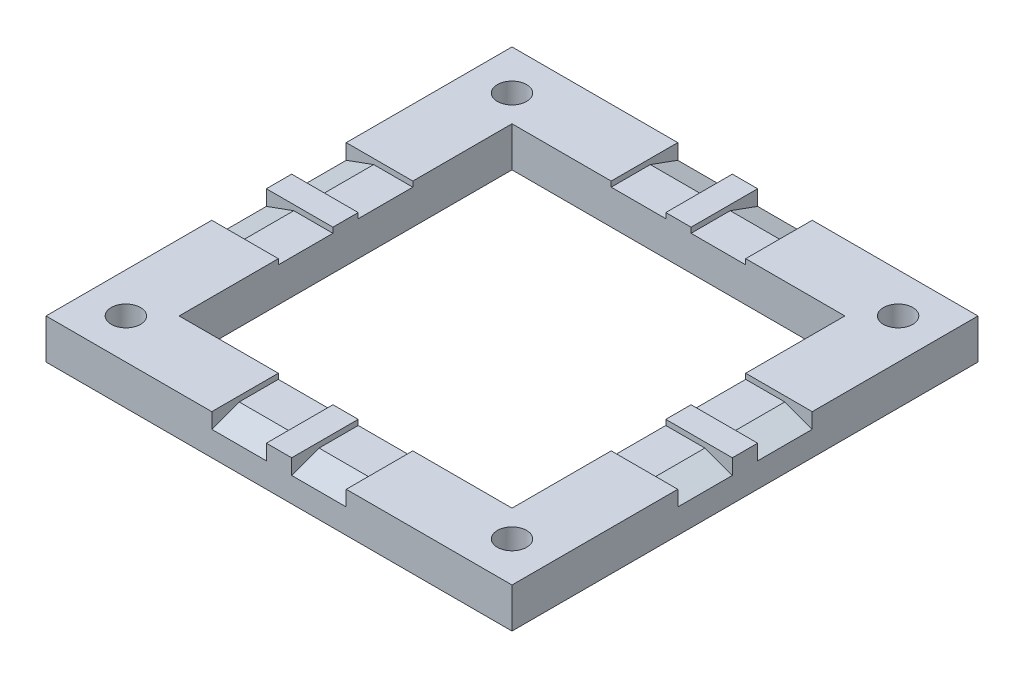
SolidWorks part; units mm, degrees
ref_plane "Front Plane" through (0, 0, 0) normal (0, 0, 1) x (1, 0, 0)
ref_plane "Top Plane" through (0, 0, 0) normal (0, 1, 0) x (1, 0, 0)
ref_plane "Right Plane" through (0, 0, 0) normal (1, 0, 0) x (0, 0, -1)
sketch "Sketch1" plane through (0, 0, 0) normal (0, 1, 0) x (1, 0, 0)
  line L1 (-17.5, -17.5) -> (17.5, -17.5)
  line L2 (-17.5, -17.5) -> (-17.5, 17.5)
  line L3 (-17.5, 17.5) -> (17.5, 17.5)
  line L4 (17.5, -17.5) -> (17.5, 17.5)
  line L5 (-17.5, -17.5) -> (17.5, 17.5) construction
  line L6 (-17.5, 17.5) -> (17.5, -17.5) construction
  point P0 (0, 0)
  dimension "D1" = 35
extrude "Boss-Extrude1" add sketch "Sketch1" along normal blind 3
sketch "Sketch3" plane through (0, 3, 0) normal (0, 1, 0) x (1, 0, 0)
  line L1 (-12.5, -12.5) -> (12.5, -12.5)
  line L2 (-12.5, -12.5) -> (-12.5, 12.5)
  line L3 (-12.5, 12.5) -> (12.5, 12.5)
  line L4 (12.5, -12.5) -> (12.5, 12.5)
  line L5 (-12.5, -12.5) -> (12.5, 12.5) construction
  line L6 (-12.5, 12.5) -> (12.5, -12.5) construction
  point P0 (0, 0)
  dimension "D1" = 25
extrude "Cut-Extrude1" cut sketch "Sketch3" against normal through all
sketch "Sketch4" plane through (0, 3, 0) normal (0, 1, 0) x (1, 0, 0)
  line L0 (-17.5, 17.5) -> (-17.5, -17.5) construction
  line L1 (-17.5, 5.05) -> (-12.5, 5.05)
  line L2 (-17.5, 5.05) -> (-17.5, 0.95)
  line L3 (-17.5, 0.95) -> (-12.5, 0.95)
  line L4 (-12.5, 5.05) -> (-12.5, 0.95)
  line L5 (-12.5, 12.5) -> (-12.5, -12.5) construction
  line L6 (17.5, 17.5) -> (-17.5, 17.5) construction
  line L7 (-5.05, 17.5) -> (-0.95, 17.5)
  line L8 (-5.05, 17.5) -> (-5.05, 12.5)
  line L9 (-5.05, 12.5) -> (-0.95, 12.5)
  line L10 (-0.95, 17.5) -> (-0.95, 12.5)
  line L11 (12.5, 12.5) -> (-12.5, 12.5) construction
  line L12 (0, 0) -> (0, 27.0615) construction
  line L13 (-23.33, 0) -> (0, 0) construction
  line L14 (0.95, 17.5) -> (0.95, 12.5)
  line L15 (5.05, 12.5) -> (0.95, 12.5)
  line L16 (5.05, 17.5) -> (5.05, 12.5)
  line L17 (5.05, 17.5) -> (0.95, 17.5)
  line L18 (12.5, 5.05) -> (12.5, 0.95)
  line L19 (17.5, 0.95) -> (12.5, 0.95)
  line L20 (17.5, 5.05) -> (17.5, 0.95)
  line L21 (17.5, 5.05) -> (12.5, 5.05)
  line L22 (17.5, -5.05) -> (12.5, -5.05)
  line L23 (17.5, -5.05) -> (17.5, -0.95)
  line L24 (17.5, -0.95) -> (12.5, -0.95)
  line L25 (12.5, -5.05) -> (12.5, -0.95)
  line L26 (5.05, -17.5) -> (0.95, -17.5)
  line L27 (5.05, -17.5) -> (5.05, -12.5)
  line L28 (5.05, -12.5) -> (0.95, -12.5)
  line L29 (0.95, -17.5) -> (0.95, -12.5)
  line L30 (-0.95, -17.5) -> (-0.95, -12.5)
  line L31 (-5.05, -12.5) -> (-0.95, -12.5)
  line L32 (-5.05, -17.5) -> (-5.05, -12.5)
  line L33 (-5.05, -17.5) -> (-0.95, -17.5)
  line L34 (-12.5, -5.05) -> (-12.5, -0.95)
  line L35 (-17.5, -0.95) -> (-12.5, -0.95)
  line L36 (-17.5, -5.05) -> (-17.5, -0.95)
  line L37 (-17.5, -5.05) -> (-12.5, -5.05)
  dimension "D1" = 1.9
  dimension "D2" = 1.9
  dimension "D3" = 4.1
extrude "Cut-Extrude2" cut sketch "Sketch4" against normal blind 0.4
chamfer "Chamfer1" distance 0.75 angle 70 8 edges at (-17.5, 2.6, -3) (-17.5, 2.6, 3) (-3, 2.6, 17.5) (3, 2.6, 17.5) (17.5, 2.6, 3) (17.5, 2.6, -3) (3, 2.6, -17.5) (-3, 2.6, -17.5)
sketch "Sketch6" plane through (0, 3, 0) normal (0, 1, 0) x (1, 0, 0)
  line L1 (-14.5, -14.5) -> (14.5, -14.5) construction
  line L2 (-14.5, -14.5) -> (-14.5, 14.5) construction
  line L3 (-14.5, 14.5) -> (14.5, 14.5) construction
  line L4 (14.5, -14.5) -> (14.5, 14.5) construction
  line L5 (-14.5, -14.5) -> (14.5, 14.5) construction
  line L6 (-14.5, 14.5) -> (14.5, -14.5) construction
  circle A0 centre (14.5, 14.5) radius 1.1
  circle A1 centre (-14.5, 14.5) radius 1.1
  circle A2 centre (-14.5, -14.5) radius 1.1
  circle A3 centre (14.5, -14.5) radius 1.1
  point P0 (0, 0)
  dimension "D2" = 2.2
  dimension "D1" = 29
extrude "Cut-Extrude5" cut sketch "Sketch6" against normal through all
sketch "Sketch7" plane through (0, 0, 0) normal (0, -1, 0) x (1, 0, 0)
  line L0 (0, 0) -> (-14.5, 14.5) construction
  line L1 (-12.867, 12.867) -> (-12.2693, 15.0977)
  line L2 (-12.2693, 15.0977) -> (-13.9023, 16.7307)
  line L3 (-13.9023, 16.7307) -> (-16.133, 16.133)
  line L4 (-16.133, 16.133) -> (-16.7307, 13.9023)
  line L5 (-16.7307, 13.9023) -> (-15.0977, 12.2693)
  line L6 (-15.0977, 12.2693) -> (-12.867, 12.867)
  line L7 (12.867, 12.867) -> (15.0977, 12.2693)
  line L8 (15.0977, 12.2693) -> (16.7307, 13.9023)
  line L9 (16.7307, 13.9023) -> (16.133, 16.133)
  line L10 (16.133, 16.133) -> (13.9023, 16.7307)
  line L11 (13.9023, 16.7307) -> (12.2693, 15.0977)
  line L12 (12.2693, 15.0977) -> (12.867, 12.867)
  line L13 (0, 0) -> (14.5, 14.5) construction
  line L14 (12.867, -12.867) -> (12.2693, -15.0977)
  line L15 (12.2693, -15.0977) -> (13.9023, -16.7307)
  line L16 (13.9023, -16.7307) -> (16.133, -16.133)
  line L17 (16.133, -16.133) -> (16.7307, -13.9023)
  line L18 (16.7307, -13.9023) -> (15.0977, -12.2693)
  line L19 (15.0977, -12.2693) -> (12.867, -12.867)
  line L20 (0, 0) -> (14.5, -14.5) construction
  line L21 (-12.867, -12.867) -> (-15.0977, -12.2693)
  line L22 (-15.0977, -12.2693) -> (-16.7307, -13.9023)
  line L23 (-16.7307, -13.9023) -> (-16.133, -16.133)
  line L24 (-16.133, -16.133) -> (-13.9023, -16.7307)
  line L25 (-13.9023, -16.7307) -> (-12.2693, -15.0977)
  line L26 (-12.2693, -15.0977) -> (-12.867, -12.867)
  line L27 (0, 0) -> (-14.5, -14.5) construction
  circle A0 centre (-14.5, 14.5) radius 2 construction
  circle A1 centre (14.5, 14.5) radius 2 construction
  circle A2 centre (14.5, -14.5) radius 2 construction
  circle A3 centre (-14.5, -14.5) radius 2 construction
  point P38 (0, 0)
  dimension "D1" = 4
extrude "Cut-Extrude6" cut sketch "Sketch7" against normal blind 1
